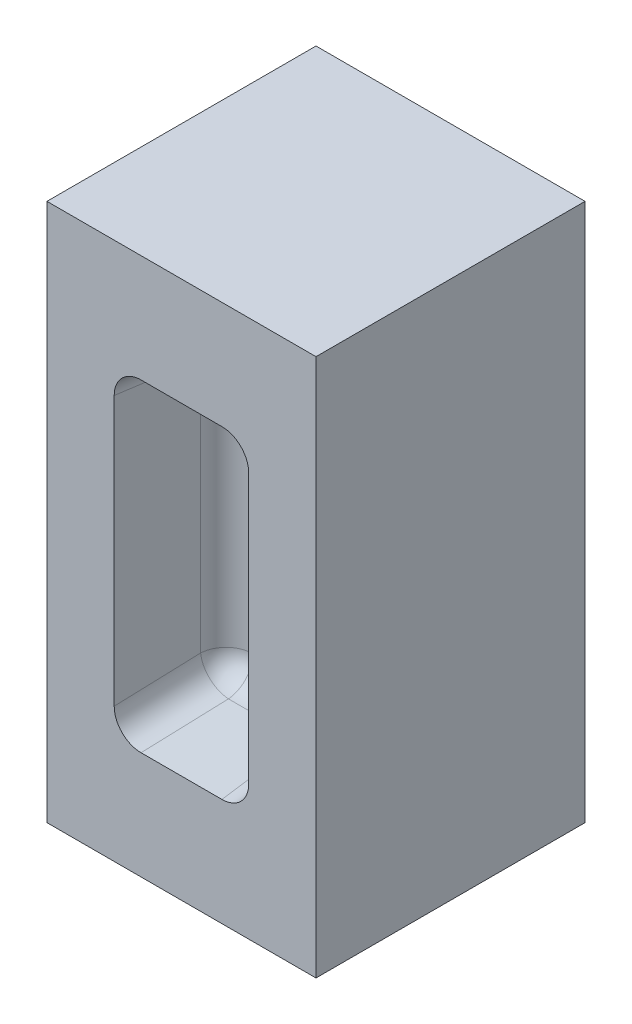
SolidWorks part; units mm, degrees
ref_plane "Ebene vorne" through (0, 0, 0) normal (0, 0, 1) x (1, 0, 0)
ref_plane "Ebene oben" through (0, 0, 0) normal (0, 1, 0) x (1, 0, 0)
ref_plane "Ebene rechts" through (0, 0, 0) normal (1, 0, 0) x (0, 0, -1)
sketch "Skizze1" plane through (0, 0, 0) normal (0, 0, 1) x (1, 0, 0)
  line L1 (0, 0) -> (50, 0)
  line L2 (0, 0) -> (0, 100)
  line L3 (0, 100) -> (50, 100)
  line L4 (50, 0) -> (50, 100)
  dimension "D1" = 100
  dimension "D2" = 50
extrude "Aufsatz-Linear austragen1" add sketch "Skizze1" along normal blind 50
sketch "Skizze2" plane through (0, 0, 50) normal (0, 0, 1) x (1, 0, 0)
  line L0 (50, 100) -> (0, 100) construction
  line L1 (12.5, 80) -> (37.5, 80)
  line L2 (12.5, 80) -> (12.5, 20)
  line L3 (12.5, 20) -> (37.5, 20)
  line L4 (37.5, 80) -> (37.5, 20)
  line L5 (25, 100) -> (25, 0) construction
  line L6 (0, 0) -> (50, 0) construction
  line L7 (0, 50) -> (50, 50) construction
  line L8 (0, 100) -> (0, 0) construction
  line L9 (50, 0) -> (50, 100) construction
  point P7 (25, 80)
  point P18 (12.5, 50)
  dimension "D1" = 60
  dimension "D2" = 25
extrude "Schnitt-Linear austragen1" cut sketch "Skizze2" against normal blind 20
draft "Formschräge1" type of draft neutral plane draft angle 3 faces to draft 2 face at (37.5, 50, 40) face at (12.5, 50, 40) neutral plane through (0, 0, 50) neutral plane normal (0, 0, 1) parameters "D1"=3
draft "Formschräge2" type of draft neutral plane draft angle 5 faces to draft 2 face at (25, 20, 40) face at (25, 80, 40) neutral plane through (0, 0, 50) neutral plane normal (0, 0, 1) parameters "D1"=5
fillet "Verrundung1" radius 5 8 edges at (25, 78.2502, 30) (36.4518, 50, 30) (25, 21.7498, 30) (13.5482, 50, 30) (13.0241, 20.8749, 40) (36.9759, 20.8749, 40) (36.9759, 79.1251, 40) (13.0241, 79.1251, 40)
sketch "Skizze3" plane through (0, 0, 50) normal (0, 0, 1) x (1, 0, 0)
  line L0 (17.484, 20) -> (32.516, 20) construction
  line L1 (12.5, 75.0038) -> (12.5, 24.9962) construction
  line L2 (32.516, 80) -> (17.484, 80) construction
  line L3 (37.5, 24.9962) -> (37.5, 75.0038) construction
  line L4 (0, 100) -> (0, 0)
  line L5 (0, 0) -> (50, 0)
  line L6 (50, 0) -> (50, 100)
  line L7 (50, 100) -> (0, 100)
  line L8 (0, 100) -> (0, 0)
  line L9 (0, 0) -> (50, 0)
  line L10 (50, 0) -> (50, 100)
  line L11 (50, 100) -> (0, 100)
  line L12 (17.484, 20) -> (32.516, 20)
  line L13 (12.5, 75.0038) -> (12.5, 24.9962)
  line L14 (32.516, 80) -> (17.484, 80)
  line L15 (37.5, 24.9962) -> (37.5, 75.0038)
  line L16 (14, 75.0038) -> (14, 24.9962)
  line L17 (17.484, 21.5) -> (32.516, 21.5)
  line L18 (36, 24.9962) -> (36, 75.0038)
  line L19 (32.516, 78.5) -> (17.484, 78.5)
  ellipse E0 centre (17.5069, 25.0191) end of major axis (20.0896, 29.3307) minor radius 5 (12.5, 24.9962) -> (17.484, 20) ccw construction
  ellipse E1 centre (17.5069, 74.9809) end of major axis (20.0896, 70.6693) minor radius 5 (17.484, 80) -> (12.5, 75.0038) ccw construction
  ellipse E2 centre (32.4931, 74.9809) end of major axis (29.9104, 70.6693) minor radius 5 (37.5, 75.0038) -> (32.516, 80) ccw construction
  ellipse E3 centre (32.4931, 25.0191) end of major axis (29.9104, 29.3307) minor radius 5 (32.516, 20) -> (37.5, 24.9962) ccw construction
  ellipse E4 centre (17.5069, 25.0191) end of major axis (20.0896, 29.3307) minor radius 5 (12.5, 24.9962) -> (17.484, 20) ccw
  ellipse E5 centre (17.5069, 74.9809) end of major axis (20.0896, 70.6693) minor radius 5 (17.484, 80) -> (12.5, 75.0038) ccw
  ellipse E6 centre (32.4931, 74.9809) end of major axis (29.9104, 70.6693) minor radius 5 (37.5, 75.0038) -> (32.516, 80) ccw
  ellipse E7 centre (32.4931, 25.0191) end of major axis (29.9104, 29.3307) minor radius 5 (32.516, 20) -> (37.5, 24.9962) ccw
  spline S0 degree 1 poles (17.484, 78.5) (14, 75.0038) knots 0 0 1 1 construction
  spline S1 degree 1 poles (14, 24.9962) (17.484, 21.5) knots 0 0 1 1 construction
  spline S2 degree 1 poles (32.516, 21.5) (36, 24.9962) knots 0 0 1 1 construction
  spline S3 degree 1 poles (36, 75.0038) (32.516, 78.5) knots 0 0 1 1 construction
  spline S4 degree 3 poles (17.484, 78.5) (17.0305, 78.5) (16.1128, 78.3184) (14.9569, 77.5427) (14.1818, 76.3828) (14, 75.4596) (14, 75.0038) knots 2.604169 2.604169 2.604169 2.604169 2.995728 3.387287 3.778845 4.170404 4.170404 4.170404 4.170404
  spline S5 degree 3 poles (14, 24.9962) (14, 24.5404) (14.1818, 23.6172) (14.9569, 22.4573) (16.1128, 21.6816) (17.0305, 21.5) (17.484, 21.5) knots 2.112781 2.112781 2.112781 2.112781 2.50434 2.895899 3.287457 3.679016 3.679016 3.679016 3.679016
  spline S6 degree 3 poles (32.516, 21.5) (32.9695, 21.5) (33.8872, 21.6816) (35.0431, 22.4573) (35.8182, 23.6172) (36, 24.5404) (36, 24.9962) knots 2.604169 2.604169 2.604169 2.604169 2.995728 3.387287 3.778845 4.170404 4.170404 4.170404 4.170404
  spline S7 degree 3 poles (36, 75.0038) (36, 75.4596) (35.8182, 76.3828) (35.0431, 77.5427) (33.8872, 78.3184) (32.9695, 78.5) (32.516, 78.5) knots 2.112781 2.112781 2.112781 2.112781 2.50434 2.895899 3.287457 3.679016 3.679016 3.679016 3.679016
  dimension "D1" = 0
  dimension "D2" = 1.5
